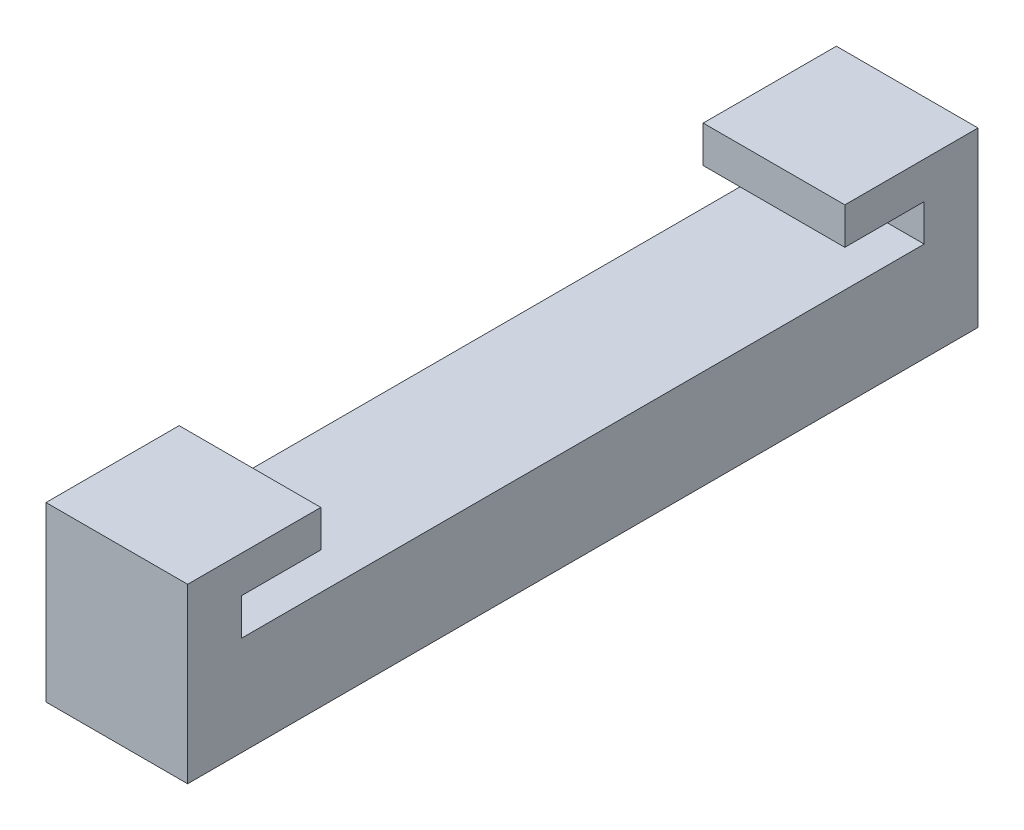
SolidWorks part; units mm, degrees
material "ABS"
ref_plane "Front Plane" through (0, 0, 0) normal (0, 0, 1) x (1, 0, 0)
ref_plane "Top Plane" through (0, 0, 0) normal (0, 1, 0) x (1, 0, 0)
ref_plane "Right Plane" through (0, 0, 0) normal (1, 0, 0) x (0, 0, -1)
sketch "Sketch1" plane through (0, 0, 0) normal (1, 0, 0) x (0, 0, -1)
  line L0 (0, 0) -> (80.01, 0)
  line L1 (80.01, 0) -> (80.01, 19.05)
  line L2 (80.01, 19.05) -> (71.12, 19.05)
  line L3 (71.12, 19.05) -> (71.12, 8.89)
  line L4 (71.12, 8.89) -> (8.89, 8.89)
  line L5 (8.89, 8.89) -> (8.89, 19.05)
  line L6 (8.89, 19.05) -> (0, 19.05)
  line L7 (0, 19.05) -> (0, 0)
  dimension "D1" = 62.23
  dimension "D2" = 8.89
  dimension "D3" = 8.89
  dimension "D4" = 8.89
  dimension "D5" = 10.16
  dimension "D6" = 10.16
extrude "Boss-Extrude1" add sketch "Sketch1" along normal blind 12.7
sketch "Sketch2" plane through (0, 0, 0) normal (-1, 0, 0) x (0, 0, 1)
  line L0 (-40.005, 8.89) -> (-63.5, 8.89) construction
  line L1 (-71.12, 8.89) -> (-8.89, 8.89) construction
  line L2 (-40.005, 8.89) -> (-16.51, 8.89) construction
  line L3 (-63.5, 8.89) -> (-63.5, 12.192) construction
  line L4 (-16.51, 8.89) -> (-16.51, 12.192) construction
  line L5 (-63.5, 12.192) -> (-70.612, 12.192)
  line L6 (-16.51, 12.192) -> (-9.398, 12.192)
  line L7 (-63.5, 12.192) -> (-63.5, 15.494)
  line L8 (-63.5, 15.494) -> (-74.93, 15.494)
  line L9 (-74.93, 15.494) -> (-74.93, 8.89)
  line L10 (-74.93, 8.89) -> (-70.612, 8.89)
  line L11 (-70.612, 8.89) -> (-70.612, 12.192)
  line L12 (-16.51, 12.192) -> (-16.51, 15.494)
  line L13 (-16.51, 15.494) -> (-5.08, 15.494)
  line L14 (-5.08, 15.494) -> (-5.08, 8.89)
  line L15 (-5.08, 8.89) -> (-9.398, 8.89)
  line L16 (-9.398, 8.89) -> (-9.398, 12.192)
  dimension "D1" = 23.495
  dimension "D2" = 23.495
  dimension "D3" = 3.302
  dimension "D4" = 3.302
  dimension "D5" = 7.112
  dimension "D6" = 7.112
  dimension "D7" = 3.302
  dimension "D8" = 11.43
  dimension "D9" = 11.43
extrude "Boss-Extrude3" add sketch "Sketch2" against normal blind 12.7
sketch "Sketch4" plane through (0, 0, 0) normal (-1, 0, 0) x (0, 0, 1)
  line L0 (-71.12, 15.494) -> (-75.438, 15.494)
  line L1 (-75.438, 15.494) -> (-75.438, 0)
  line L2 (0, 0) -> (-80.01, 0) construction
  line L3 (-75.438, 0) -> (-80.01, 0)
  line L4 (-80.01, 0) -> (-80.01, 19.05)
  line L5 (-80.01, 19.05) -> (-71.12, 19.05)
  line L6 (-71.12, 19.05) -> (-71.12, 15.494)
  dimension "D1" = 4.318
extrude "Cut-Extrude1" cut sketch "Sketch4" against normal up to next
sketch "Sketch5" plane through (0, 0, 0) normal (-1, 0, 0) x (0, 0, 1)
  line L0 (-8.89, 15.494) -> (-4.572, 15.494)
  line L1 (-4.572, 15.494) -> (-4.572, 0)
  line L2 (0, 0) -> (-75.438, 0) construction
  line L3 (-4.572, 0) -> (0, 0)
  line L4 (0, 0) -> (0, 19.05)
  line L5 (0, 19.05) -> (-8.89, 19.05)
  line L6 (-8.89, 19.05) -> (-8.89, 15.494)
  dimension "D1" = 4.318
extrude "Cut-Extrude2" cut sketch "Sketch5" against normal up to next
sketch "Sketch6" plane through (12.7, 0, 0) normal (1, 0, 0) x (0, 0, -1)
  line L0 (16.51, 12.192) -> (16.51, 8.89)
  line L1 (70.612, 8.89) -> (9.398, 8.89) construction
  line L2 (16.51, 8.89) -> (9.398, 8.89)
  line L3 (9.398, 8.89) -> (9.398, 12.192)
  line L4 (9.398, 12.192) -> (16.51, 12.192)
extrude "Boss-Extrude4" add sketch "Sketch6" against normal blind 3.175
sketch "Sketch7" plane through (12.7, 0, 0) normal (1, 0, 0) x (0, 0, -1)
  line L0 (63.5, 12.192) -> (63.5, 8.89)
  line L1 (70.612, 8.89) -> (16.51, 8.89) construction
  line L2 (63.5, 8.89) -> (70.612, 8.89)
  line L3 (70.612, 8.89) -> (70.612, 12.192)
  line L4 (70.612, 12.192) -> (63.5, 12.192)
extrude "Boss-Extrude5" add sketch "Sketch7" against normal blind 3.175
sketch "Sketch8" plane through (12.7, 0, 0) normal (1, 0, 0) x (0, 0, -1)
  line L0 (16.51, 8.89) -> (16.51, 12.192)
  line L1 (16.51, 15.494) -> (16.51, 8.89) construction
  line L2 (16.51, 12.192) -> (9.398, 12.192)
  line L3 (9.398, 12.192) -> (9.398, 8.89)
  line L4 (9.398, 8.89) -> (16.51, 8.89)
  dimension "D1" = 7.112
extrude "Cut-Extrude3" cut sketch "Sketch8" against normal up to next
sketch "Sketch9" plane through (12.7, 0, 0) normal (1, 0, 0) x (0, 0, -1)
  line L0 (63.5, 8.89) -> (63.5, 12.192)
  line L1 (63.5, 8.89) -> (63.5, 15.494) construction
  line L2 (63.5, 12.192) -> (70.612, 12.192)
  line L3 (70.612, 12.192) -> (70.612, 8.89)
  line L4 (70.612, 8.89) -> (63.5, 8.89)
  dimension "D1" = 7.112
extrude "Cut-Extrude4" cut sketch "Sketch9" against normal up to next
